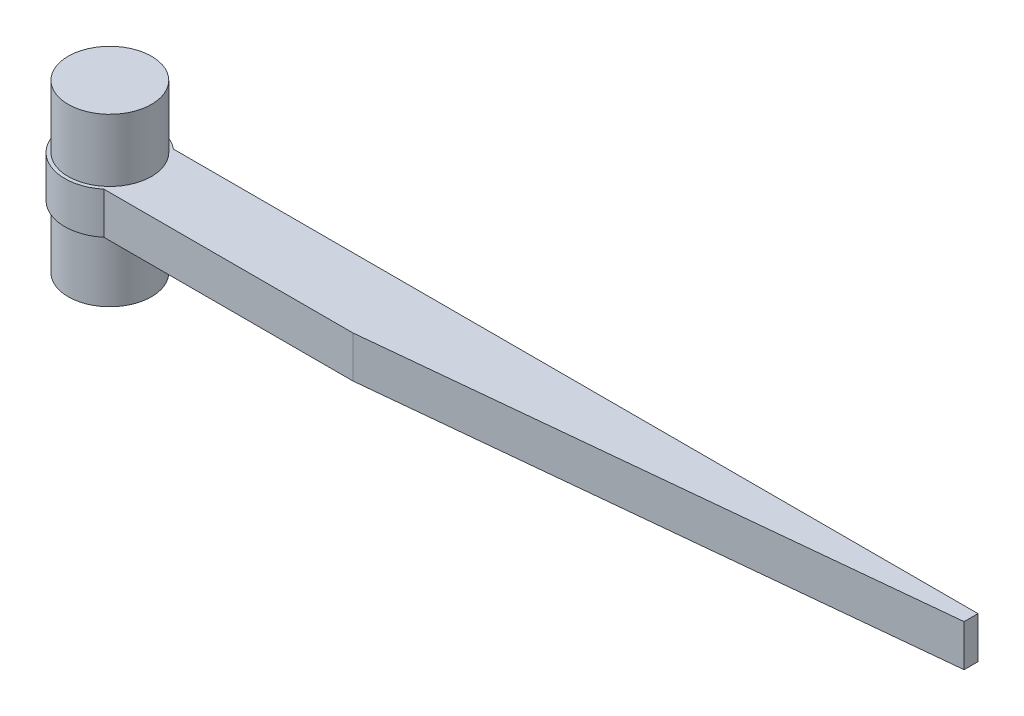
SolidWorks part; units mm, degrees
ref_plane "Front Plane" through (0, 0, 0) normal (0, 0, 1) x (1, 0, 0)
ref_plane "Top Plane" through (0, 0, 0) normal (0, 1, 0) x (1, 0, 0)
ref_plane "Right Plane" through (0, 0, 0) normal (1, 0, 0) x (0, 0, -1)
sketch "Sketch1" plane through (0, 0, 0) normal (0, 1, 0) x (1, 0, 0)
  circle A0 centre (0, 0) radius 3.25
  dimension "D1" = 6.5
extrude "Boss-Extrude1" add sketch "Sketch1" along normal mid plane 3
sketch "Sketch2" plane through (0, 0, 0) normal (0, 1, 0) x (1, 0, 0)
  circle A0 centre (0, 0) radius 3
  dimension "D1" = 6
extrude "Boss-Extrude2" add sketch "Sketch2" along normal mid plane 12
sketch "Sketch3" plane through (0, 0, 0) normal (0, 0, 1) x (1, 0, 0)
  line L0 (3.25, 1.5) -> (-3.25, 1.5) construction
  line L1 (0, 1.5) -> (60, 1.5)
  line L2 (0, 1.5) -> (0, -1.5)
  line L3 (0, -1.5) -> (60, -1.5)
  line L4 (60, 1.5) -> (60, -1.5)
  line L6 (-3, -1.5) -> (3, -1.5) construction
  dimension "D1" = 60
extrude "Boss-Extrude3" add sketch "Sketch3" along normal mid plane 5
chamfer "Chamfer1" distance 4 distance2 40 1 edges at (60, 0, 2.5)
sketch "Sketch4" plane through (0, 0, -2.5) normal (0, 0, -1) x (-1, 0, 0)
  circle A0 centre (-6.0447, 0) radius 0.85
  circle A1 centre (-11.0447, 0) radius 0.85
  circle A2 centre (-16.0447, 0) radius 0.85
  circle A3 centre (-21.0447, 0) radius 0.85
  circle A4 centre (-26.0447, 0) radius 0.85
  circle A5 centre (-31.0447, 0) radius 0.85
  circle A6 centre (-36.0447, 0) radius 0.85
  circle A7 centre (-41.0447, 0) radius 0.85
  circle A8 centre (-46.0447, 0) radius 0.85
  circle A9 centre (-51.0447, 0) radius 0.85
  circle A10 centre (-56.0447, 0) radius 0.85
  dimension "D1" = 1.7
  dimension "D2" = 11
extrude "Cut-Extrude1" cut sketch "Sketch4" against normal blind 0.5
